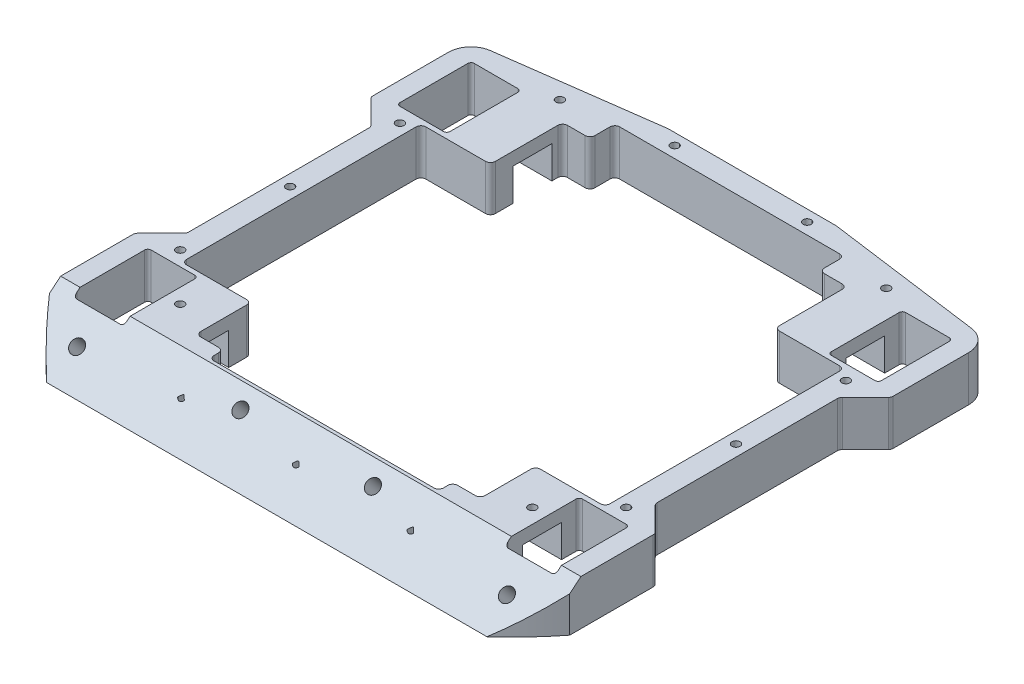
SolidWorks part; units mm, degrees
material "7075-T6, Plate (SS)"
ref_plane "Front Plane" through (0, 0, 0) normal (0, 0, 1) x (1, 0, 0)
ref_plane "Top Plane" through (0, 0, 0) normal (0, 1, 0) x (1, 0, 0)
ref_plane "Right Plane" through (0, 0, 0) normal (1, 0, 0) x (0, 0, -1)
sketch "Sketch1" plane through (0, 0, 0) normal (0, 1, 0) x (1, 0, 0)
  line L0 (0, 0) -> (0, 74) construction
  line L1 (-80.5, -80.75) -> (80.5, -80.75)
  line L2 (-80.5, -80.75) -> (-80.5, 74)
  line L3 (-80.5, 74) -> (80.5, 74)
  line L4 (80.5, -80.75) -> (80.5, 74)
  point P0 (0, 0)
  dimension "D1" = 80.75
  dimension "D2" = 161
  dimension "D3" = 74
extrude "outline" add sketch "Sketch1" along normal blind 14
sketch "Sketch2" plane through (0, 14, 0) normal (0, 1, 0) x (1, 0, 0)
  line L1 (-35.5, 67) -> (35.5, 67)
  line L2 (65.5, 37) -> (65.5, -37)
  line L3 (-35.5, -58.5) -> (35.5, -58.5)
  line L4 (-59, 38.5) -> (-59, 61.5)
  line L6 (0, 0) -> (0, 63.7455) construction
  line L7 (35.5, 67) -> (35.5, 37)
  line L8 (35.5, 37) -> (65.5, 37)
  line L9 (-74.5, 61.5) -> (-74.5, 38.5)
  line L11 (-59, 61.5) -> (-74.5, 61.5)
  line L12 (-74.5, 38.5) -> (-59, 38.5)
  line L13 (-35.5, 37) -> (-65.5, 37)
  line L14 (-35.5, 67) -> (-35.5, 37)
  line L15 (0, 0) -> (-65.5, 0) construction
  line L17 (59, 61.5) -> (74.5, 61.5)
  line L18 (74.5, 61.5) -> (74.5, 38.5)
  line L19 (74.5, 38.5) -> (59, 38.5)
  line L20 (59, -38.5) -> (59, -61.5)
  line L21 (74.5, -38.5) -> (59, -38.5)
  line L22 (74.5, -61.5) -> (74.5, -38.5)
  line L23 (59, -61.5) -> (74.5, -61.5)
  line L24 (-65.5, 37) -> (-65.5, -37)
  line L25 (35.5, -37) -> (65.5, -37)
  line L26 (35.5, -58.5) -> (35.5, -37)
  line L27 (-35.5, -58.5) -> (-35.5, -37)
  line L28 (-35.5, -37) -> (-65.5, -37)
  line L29 (-74.5, -38.5) -> (-59, -38.5)
  line L30 (59, 38.5) -> (59, 61.5)
  line L31 (-59, -61.5) -> (-74.5, -61.5)
  line L32 (-74.5, -61.5) -> (-74.5, -38.5)
  line L33 (-59, -38.5) -> (-59, -61.5)
  point P21 (74.5, 50)
  point P36 (65.5, 0)
  dimension "D1" = 23
  dimension "D2" = 15.5
  dimension "D3" = 23.5
  dimension "D4" = 74
  dimension "D6" = 65.5
  dimension "D7" = 35.5
  dimension "D9" = 50
  dimension "D10" = 67
  dimension "D11" = 58.5
  dimension "D12" = 71
extrude "thru-all" cut sketch "Sketch2" against normal through all
sketch "Sketch14" plane through (0, 14, 0) normal (0, 1, 0) x (1, 0, 0)
  line L1 (43.9886, -54.1431) -> (-43.9886, -54.1431)
  line L2 (43.9886, -54.1431) -> (43.9886, 59.3307)
  line L3 (43.9886, 59.3307) -> (-43.9886, 59.3307)
  line L4 (-43.9886, -54.1431) -> (-43.9886, 59.3307)
  line L5 (43.9886, -54.1431) -> (-43.9886, 59.3307) construction
  line L6 (43.9886, 59.3307) -> (-43.9886, -54.1431) construction
  point P0 (0, 2.5938)
extrude "lazy extra" cut sketch "Sketch14" against normal through all
sketch "Sketch3" plane through (0, 0, 0) normal (0, -1, 0) x (1, 0, 0)
  line L0 (-59, 61.5) -> (-59, 38.5) construction
  line L1 (-59, 56) -> (-35.5, 56)
  line L2 (-59, 56) -> (-59, 44)
  line L3 (-59, 44) -> (-35.5, 44)
  line L4 (-35.5, 56) -> (-35.5, 44)
  line L5 (-35.5, 54.1431) -> (-35.5, 58.5) construction
  line L7 (0, 38.8516) -> (0, 0) construction
  line L8 (0, 0) -> (-29.8777, 0) construction
  line L9 (35.5, 56) -> (35.5, 44)
  line L10 (59, 44) -> (35.5, 44)
  line L11 (59, 56) -> (59, 44)
  line L12 (59, 56) -> (35.5, 56)
  line L13 (59, -56) -> (35.5, -56)
  line L14 (59, -56) -> (59, -44)
  line L15 (59, -44) -> (35.5, -44)
  line L16 (35.5, -56) -> (35.5, -44)
  line L17 (-35.5, -56) -> (-35.5, -44)
  line L18 (-59, -44) -> (-35.5, -44)
  line L19 (-59, -56) -> (-59, -44)
  line L20 (-59, -56) -> (-35.5, -56)
  line L21 (-65.5, 37) -> (-43.9886, 37) construction
  dimension "D1" = 12
  dimension "D2" = 7
extrude "motor huts" cut sketch "Sketch3" against normal blind 10
fillet "wheel well" radius 1 16 edges at (74.5, 7, -38.5) (59, 7, -38.5) (74.5, 7, -61.5) (59, 7, -61.5) (-59, 7, -38.5) (-59, 7, -61.5) (-74.5, 7, -38.5) (-74.5, 7, -61.5) (74.5, 7, 61.5) (59, 7, 61.5) (74.5, 7, 38.5) (59, 7, 38.5) (-59, 7, 61.5) (-74.5, 7, 61.5) (-74.5, 7, 38.5) (-59, 7, 38.5)
sketch "Sketch5" plane through (0, 14, 0) normal (0, 1, 0) x (1, 0, 0)
  line L0 (-80.5, 36.5) -> (-72.5, 28.5)
  line L1 (-80.5, 74) -> (-80.5, -80.75) construction
  line L2 (-72.5, 28.5) -> (-72.5, -28.5)
  line L3 (-72.5, -28.5) -> (-80.5, -36.5)
  line L4 (0, 0) -> (-72.5, 0) construction
  line L5 (-65.5, 37) -> (-65.5, -37) construction
  line L6 (-73.5, 38.5) -> (-60, 38.5) construction
  line L7 (-80.5, 36.5) -> (-80.5, -36.5)
  line L10 (-74.4399, 67.4366) -> (-26, 74)
  line L11 (80.5, 74) -> (-80.5, 74) construction
  line L13 (-80.5, 60.5) -> (-88.2369, 60.5)
  line L14 (-88.2369, 60.5) -> (-88.2369, 78.2375)
  line L15 (-88.2369, 78.2375) -> (-26, 78.2375)
  line L16 (-26, 78.2375) -> (-26, 74)
  line L17 (0, 0) -> (0, 48.1732) construction
  line L18 (26, 78.2375) -> (26, 74)
  line L19 (88.2369, 78.2375) -> (26, 78.2375)
  line L20 (88.2369, 60.5) -> (88.2369, 78.2375)
  line L21 (80.5, 60.5) -> (88.2369, 60.5)
  line L22 (74.4399, 67.4366) -> (26, 74)
  line L23 (80.5, 36.5) -> (80.5, -36.5)
  line L24 (72.5, -28.5) -> (80.5, -36.5)
  line L25 (72.5, 28.5) -> (72.5, -28.5)
  line L26 (80.5, 36.5) -> (72.5, 28.5)
  arc A0 (-80.5, 60.5) -> (-74.4399, 67.4366) centre (-73.5, 60.5) cw
  arc A1 (-73.5, 61.5) -> (-74.5, 60.5) centre (-73.5, 60.5) ccw construction
  arc A4 (80.5, 60.5) -> (74.4399, 67.4366) centre (73.5, 60.5) ccw
  dimension "D1" = 7
  dimension "D2" = 2
  dimension "D7" = 52
extrude "outer cutouts" cut sketch "Sketch5" against normal through all
sketch "Sketch13" plane through (0, 14, 0) normal (0, 1, 0) x (1, 0, 0)
  circle A0 centre (0, 0) radius 102.1972
  arc A1 (80.5, 60.5) -> (74.4399, 67.4366) centre (73.5, 60.5) ccw construction
  circle A2 centre (0, 0) radius 119.1594
extrude "Cut-Extrude1" cut sketch "Sketch13" against normal through all
fillet "fillet the rest" radius 1.5 28 edges at (-80.5, 7, -36.5) (-72.5, 7, -28.5) (-72.5, 7, 28.5) (-80.5, 7, 36.5) (80.5, 7, 36.5) (72.5, 7, 28.5) (72.5, 7, -28.5) (80.5, 7, -36.5) (65.5, 7, 37) (-65.5, 7, 37) (-65.5, 7, -37) (65.5, 7, -37) (-35.5, 7, 58.5) (35.5, 7, 58.5) (-35.5, 7, -67) (35.5, 7, -67) (43.9886, 12, 54.1431) (35.5, 12, 54.1431) (43.9886, 7, 37) (43.9886, 7, -59.3307) (43.9886, 7, -37) (35.5, 7, -59.3307) (-35.5, 12, 54.1431) (-43.9886, 12, 54.1431) (-43.9886, 7, 37) (-35.5, 7, -59.3307) (-43.9886, 7, -37) (-43.9886, 7, -59.3307)
sketch "Sketch4" plane through (80.5, 0, 0) normal (1, 0, 0) x (0, 0, -1)
  line L0 (-59.5, 14) -> (-76.1846, 0)
  line L1 (-80.75, 14) -> (74, 14) construction
  line L2 (-76.1846, 0) -> (-76.1846, 14) construction
  line L3 (-76.1846, 14) -> (-59.5, 14)
  line L4 (-80.75, 0) -> (74, 0) construction
  line L5 (-76.1846, 14) -> (-154.6436, 14)
  line L6 (-154.6436, 14) -> (-154.6436, 0)
  line L7 (-154.6436, 0) -> (-76.1846, 0)
  dimension "D1" = 40
  dimension "D2" = 1
extrude "wedge cut" cut sketch "Sketch4" against normal through all
hole_wizard "top screws" positions "Sketch7" profile "Sketch6" tap size "M3x0.5" standard "ANSI Metric"
sketch "Sketch7" plane through (0, 14, 0) normal (0, 1, 0) x (1, 0, 0)
  line L1 (-64, -37) -> (-45.4886, -37) construction
  line L3 (-35.5, -55.6431) -> (-35.5, -57) construction
  line L4 (-65.5, 35.5) -> (-65.5, -35.5) construction
  line L5 (0, 0) -> (-65.5, 0) construction
  line L7 (0, 0) -> (0, -84.2849) construction
  line L9 (26, 74) -> (-26, 74) construction
  line L10 (-80.5, 60.5) -> (-80.5, 37.1213) construction
  point P4 (-69, -34)
  point P6 (-69, 0)
  point P13 (-54.5, -48.5)
  point P52 (54.5, -48.5)
  point P54 (69, 0)
  point P55 (69, -34)
  point P58 (69, 34)
  point P65 (-69, 34)
  point P67 (-50.5, 65)
  point P69 (-20.5, 70.5)
  point P77 (20.5, 70.5)
  point P78 (50.5, 65)
  dimension "D2" = 11.5
  dimension "D3" = 19
  dimension "D4" = 3
  dimension "D6" = 3.5
  dimension "D9" = 3.5
  dimension "D10" = 9
  dimension "D11" = 60
  dimension "D12" = 30
sketch "Sketch6" plane through (-69, 14, 34) normal (1, 0, 0) x (0, 0, 1)
  line L0 (0, 0) -> (0, 7.2511)
  line L1 (0, 7.2511) -> (1.25, 6.5)
  line L2 (1.25, 6.5) -> (1.25, 0)
  line L5 (1.25, 0) -> (0, 0)
  line L10 (0, 7.2511) -> (-1.25, 6.5) construction
  line L11 (0, -6.35) -> (0, 107.95) construction
  dimension "Tap Drill Dia." = 2.5
  dimension "Tap Drill Depth" = 6.5
  dimension "Drill Angle" = 118
cosmetic thread "Hole Thread2" parameters "D1"=5, "D2"=3
cosmetic thread "Hole Thread5" parameters "D1"=5, "D2"=3
cosmetic thread "Hole Thread7" parameters "D1"=5, "D2"=3
cosmetic thread "Hole Thread8" parameters "D1"=5, "D2"=3
cosmetic thread "Hole Thread9" parameters "D1"=5, "D2"=3
cosmetic thread "Hole Thread10" parameters "D1"=5, "D2"=3
cosmetic thread "Hole Thread23" parameters "D1"=5, "D2"=3
cosmetic thread "Hole Thread25" parameters "D1"=5, "D2"=3
cosmetic thread "Hole Thread57" parameters "D1"=5, "D2"=3
cosmetic thread "Hole Thread58" parameters "D1"=5, "D2"=3
cosmetic thread "Hole Thread59" parameters "D1"=5, "D2"=3
cosmetic thread "Hole Thread60" parameters "D1"=5, "D2"=3
hole_wizard "bottom screws" positions "Sketch9" profile "Sketch8" tap size "M3x0.5" standard "ANSI Metric"
sketch "Sketch9" plane through (0, 0, 0) normal (0, -1, 0) x (-1, 0, 0)
  line L0 (64, -37) -> (45.4886, -37) construction
  line L1 (80.5, -37.1213) -> (80.5, -62.9604) construction
  line L5 (72.5, -27.8787) -> (72.5, 27.8787) construction
  line L6 (-46.8906, 0) -> (0, 0) construction
  line L7 (0, 0) -> (0, -47.6286) construction
  line L8 (-26, 74) -> (26, 74) construction
  line L9 (80.5, 60.5) -> (80.5, 37.1213) construction
  line L10 (34, -58.5) -> (-34, -58.5) construction
  line L11 (80.5, -62.9604) -> (80.5, -59.5) construction
  point P2 (35.5, -66.5)
  point P9 (69, -24)
  point P11 (55.5, -40.5)
  point P13 (55.5, -59.5)
  point P26 (0, -66.5)
  point P72 (-55.5, -59.5)
  point P73 (-55.5, -40.5)
  point P74 (-69, -24)
  point P76 (-35.5, -66.5)
  point P79 (-69, 24)
  point P80 (-55.5, 40.5)
  point P81 (-55.5, 59.5)
  point P83 (40.5, 67)
  point P84 (55.5, 59.5)
  point P85 (55.5, 40.5)
  point P86 (69, 24)
  point P90 (0, 70.5)
  point P109 (-40.5, 67)
  dimension "D1" = 3.5
  dimension "D2" = 22.5
  dimension "D3" = 8
  dimension "D4" = 25
  dimension "D5" = 45
  dimension "D8" = 3.5
  dimension "D9" = 13
  dimension "D10" = 7
  dimension "D11" = 3.5
  dimension "D12" = 40
sketch "Sketch8" plane through (-35.5, 0, 66.5) normal (1, 0, 0) x (0, 0, -1)
  line L0 (0, 0) -> (0, 8.2511)
  line L1 (0, 8.2511) -> (1.25, 7.5)
  line L2 (1.25, 7.5) -> (1.25, 0)
  line L5 (1.25, 0) -> (0, 0)
  line L10 (0, 8.2511) -> (-1.25, 7.5) construction
  line L11 (0, -6.35) -> (0, 107.95) construction
  dimension "Tap Drill Dia." = 2.5
  dimension "Tap Drill Depth" = 7.5
  dimension "Drill Angle" = 118
cosmetic thread "Hole Thread26" parameters "D1"=6, "D2"=3
cosmetic thread "Hole Thread30" parameters "D1"=6, "D2"=3
cosmetic thread "Hole Thread32" parameters "D1"=6, "D2"=3
cosmetic thread "Hole Thread33" parameters "D1"=6, "D2"=3
cosmetic thread "Hole Thread34" parameters "D1"=6, "D2"=3
cosmetic thread "Hole Thread35" parameters "D1"=6, "D2"=3
cosmetic thread "Hole Thread36" parameters "D1"=6, "D2"=3
cosmetic thread "Hole Thread37" parameters "D1"=6, "D2"=3
cosmetic thread "Hole Thread38" parameters "D1"=6, "D2"=3
cosmetic thread "Hole Thread41" parameters "D1"=6, "D2"=3
cosmetic thread "Hole Thread43" parameters "D1"=6, "D2"=3
cosmetic thread "Hole Thread44" parameters "D1"=6, "D2"=3
cosmetic thread "Hole Thread45" parameters "D1"=6, "D2"=3
cosmetic thread "Hole Thread49" parameters "D1"=6, "D2"=3
cosmetic thread "Hole Thread51" parameters "D1"=6, "D2"=3
cosmetic thread "Hole Thread52" parameters "D1"=6, "D2"=3
cosmetic thread "Hole Thread53" parameters "D1"=6, "D2"=3
cosmetic thread "Hole Thread55" parameters "D1"=6, "D2"=3
hole_wizard "M5x0.8 Tapped Hole1" positions "Sketch12" profile "Sketch10" tap size "M5x0.8" standard "ANSI Metric"
sketch "Sketch12" plane through (0, 37.5136, 31.4776) normal (0, 0.766, 0.6428) x (1, 0, 0)
  line L0 (80.5, -41.0978) -> (80.5, -36.5806) construction
  line L1 (60, -39.1914) -> (73.5, -39.1914) construction
  line L2 (-34, -35.2752) -> (34, -35.2752) construction
  line L3 (-80.5, -41.0978) -> (-80.5, -36.5806) construction
  point P0 (-66.5, -48.1914)
  point P2 (-20.5, -42.2752)
  point P4 (20.5, -42.2752)
  point P6 (66.5, -48.1914)
  dimension "D1" = 14
  dimension "D2" = 9
  dimension "D3" = 7
  dimension "D4" = 60
  dimension "D5" = 60
  dimension "D6" = 14
sketch "Sketch10" plane through (-66.5, 6.5367, 68.3944) normal (1, 0, 0) x (0, -0.6428, 0.766)
  line L0 (0, 0) -> (0, 8.6618)
  line L1 (0, 8.6618) -> (2.1, 7.4)
  line L2 (2.1, 7.4) -> (2.1, 0)
  line L5 (2.1, 0) -> (0, 0)
  line L10 (0, 8.6618) -> (-2.1, 7.4) construction
  line L11 (0, -6.35) -> (0, 107.95) construction
  dimension "Tap Drill Dia." = 4.2
  dimension "Tap Drill Depth" = 7.4
  dimension "Drill Angle" = 118
cosmetic thread "Hole Thread61" parameters "D1"=5, "D2"=5
cosmetic thread "Hole Thread62" parameters "D1"=5, "D2"=5
cosmetic thread "Hole Thread63" parameters "D1"=5, "D2"=5
cosmetic thread "Hole Thread64" parameters "D1"=5, "D2"=5
